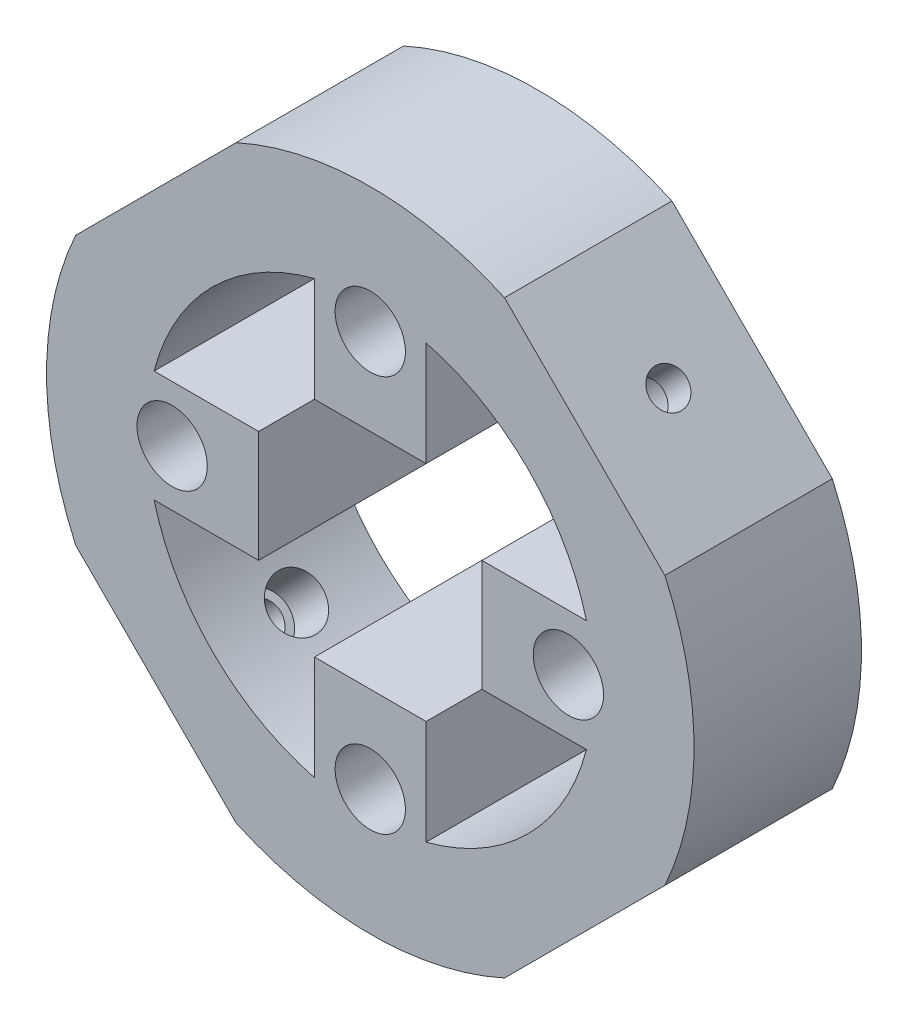
SolidWorks part; units mm, degrees
ref_plane "Front Plane" through (0, 0, 0) normal (0, 0, 1) x (1, 0, 0)
ref_plane "Top Plane" through (0, 0, 0) normal (0, 1, 0) x (1, 0, 0)
ref_plane "Right Plane" through (0, 0, 0) normal (1, 0, 0) x (0, 0, -1)
sketch "Sketch6" plane through (0, 0, 0) normal (0, 0, 1) x (1, 0, 0)
  circle A0 centre (0, 0) radius 20
  circle A1 centre (0, 0) radius 29
  dimension "D1" = 40
  dimension "D2" = 58
extrude "Inner Ring" add sketch "Sketch6" against normal blind 15 separate body
sketch "Sketch7" plane through (0, 0, 0) normal (0, 0, 1) x (1, 0, 0)
  line L2 (-10, 5) -> (-10, -5)
  line L3 (-5, 10) -> (5, 10)
  line L4 (10, 5) -> (10, -5)
  line L5 (-5, -10) -> (5, -10)
  line L14 (-19.3649, 5) -> (-10, 5)
  line L15 (-19.3649, -5) -> (-10, -5)
  line L16 (-5, 19.3649) -> (-5, 10)
  line L17 (5, 19.3649) -> (5, 10)
  line L18 (19.3649, 5) -> (10, 5)
  line L19 (19.3649, -5) -> (10, -5)
  line L20 (5, -19.3649) -> (5, -10)
  line L21 (-5, -19.3649) -> (-5, -10)
  circle A1 centre (0, 0) radius 20
  circle M19 centre (0, 0) radius 20
  dimension "D1" = 20
  dimension "D2" = 20
  dimension "D3" = 10
  dimension "D5" = 10
  dimension "D7" = 10
  dimension "D8" = 10
extrude "Motor Connector Cut" add sketch "Sketch7" against normal blind 15 contours L19 L18 L4 M19 | L17 L16 L3 M19 | L15 L2 L14 M19 | L21 L20 L5 M19
sketch "Sketch9" plane through (0, 0, -15) normal (0, 0, -1) x (-1, 0, 0)
  line L0 (-5, 19.3649) -> (-19.3649, 5)
  line L7 (-5, -19.3649) -> (-19.3649, -5)
  line L8 (5, 19.3649) -> (19.3649, 5)
  line L9 (5, -19.3649) -> (19.3649, -5)
  line L10 (19.3649, -5) -> (26.3895, -12.0246)
  line L11 (5, -19.3649) -> (12.0246, -26.3895)
  line L12 (-19.3649, -5) -> (-26.3895, -12.0246)
  line L13 (-5, -19.3649) -> (-12.0246, -26.3895)
  line L14 (-19.3649, 5) -> (-5, 19.3649)
  line L15 (-5, 19.3649) -> (-12.0246, 26.3895)
  line L16 (-19.3649, 5) -> (-26.3895, 12.0246)
  line L17 (-26.3895, 12.0246) -> (-12.0246, 26.3895)
  line L18 (-26.3895, -12.0246) -> (-12.0246, -26.3895)
  line L19 (12.0246, -26.3895) -> (26.3895, -12.0246)
  line L20 (5, 19.3649) -> (12.0246, 26.3895)
  line L21 (19.3649, 5) -> (26.3895, 12.0246)
  line L22 (26.3895, 12.0246) -> (12.0246, 26.3895)
  circle A2 centre (0, 0) radius 29
  circle A3 centre (0, 0) radius 20
  circle M28 centre (0, 0) radius 29
sketch "Sketch10" plane through (0, 0, -15) normal (0, 0, -1) x (-1, 0, 0)
  circle A3 centre (-17.75, 0) radius 3.15
  circle A4 centre (0, 17.75) radius 3.15
  circle A5 centre (17.75, 0) radius 3.15
  circle A6 centre (0, -17.75) radius 3.15
  dimension "D1" = 6.3
  dimension "D2" = 6.3
  dimension "D4" = 6.3
  dimension "D5" = 6.3
extrude "Cut-Extrude2" cut sketch "Sketch10" against normal blind 70 and the other way blind 55
extrude "Cut-Extrude4" cut sketch "Sketch9" against normal blind 22 contours L17 M28 | L22 M28 | L18 M28 | L19 M28 | A2
sketch "Sketch16" plane through (-19.2071, 19.2071, 0) normal (-0.7071, 0.7071, 0) x (0, 0, 1)
  line L0 (-7.5, 10.1575) -> (-7.5, -10.1575)
  line L1 (0, 10.1575) -> (-15, 10.1575) construction
  line L2 (0, -10.1575) -> (-15, -10.1575) construction
  circle A0 centre (-7.5, 0) radius 2.35
  dimension "D1" = 4.7
extrude "Cut-Extrude6" cut sketch "Sketch16" against normal blind 7.9 contours L0 A0 | L0 A0
sketch "Sketch14" plane through (19.2071, 19.2071, 0) normal (0.7071, 0.7071, 0) x (0, 0, -1)
  line L0 (7.5, 10.1575) -> (7.5, -10.1575)
  line L1 (0, 10.1575) -> (15, 10.1575) construction
  line L2 (0, -10.1575) -> (15, -10.1575) construction
  circle A0 centre (7.5, 0) radius 2.35
  dimension "D1" = 4.7
extrude "Cut-Extrude5" cut sketch "Sketch14" against normal blind 22 contours L0 A0 | L0 A0
sketch "Sketch15" plane through (19.2071, 19.2071, 0) normal (0.7071, 0.7071, 0) x (0, 0, -1)
  line L0 (7.5, 10.1575) -> (7.5, -10.1575)
  line L1 (0, 10.1575) -> (15, 10.1575) construction
  line L2 (0, -10.1575) -> (15, -10.1575) construction
  circle A0 centre (7.5, 0) radius 2.35
  circle A1 centre (7.5, 0) radius 1.65
  circle M1 centre (7.5, 0) radius 2.35
  dimension "D1" = 3.3
extrude "Boss-Extrude1" add sketch "Sketch15" against normal blind 2.9 contours A1 L0 M1 | A1 L0 M1
sketch "Sketch17" plane through (-19.2071, 19.2071, 0) normal (-0.7071, 0.7071, 0) x (0, 0, 1)
  line L0 (-7.5, 2.35) -> (-7.5, -2.35)
  circle A1 centre (-7.5, 0) radius 2.35 construction
  circle A2 centre (-7.5, 0) radius 2.35
  circle A3 centre (-7.5, 0) radius 1.65
  circle M1 centre (-7.5, 0) radius 2.35
  dimension "D1" = 3.3
extrude "Boss-Extrude3" add sketch "Sketch17" against normal blind 2.9 contours A3 L0 M1 | A3 L0 M1
sketch "Sketch20" plane through (-19.2071, -19.2071, 0) normal (-0.7071, -0.7071, 0) x (0, 0, 1)
  line L0 (-7.5, 10.1575) -> (-7.5, -10.1575)
  line L1 (0, 10.1575) -> (-15, 10.1575) construction
  line L2 (0, -10.1575) -> (-15, -10.1575) construction
  circle A0 centre (-7.5, 0) radius 2.35
  dimension "D1" = 4.7
extrude "Cut-Extrude8" cut sketch "Sketch20" against normal blind 9.9 contours L0 A0 | L0 A0
sketch "Sketch18" plane through (19.2071, -19.2071, 0) normal (0.7071, -0.7071, 0) x (0, 0, -1)
  line L0 (7.5, 10.1575) -> (7.5, -10.1575)
  line L1 (0, 10.1575) -> (15, 10.1575) construction
  line L2 (0, -10.1575) -> (15, -10.1575) construction
  circle A0 centre (7.5, 0) radius 2.35
  dimension "D1" = 4.7
extrude "Cut-Extrude7" cut sketch "Sketch18" against normal blind 8.9 contours L0 A0 | L0 A0
sketch "Sketch21" plane through (-19.2071, -19.2071, 0) normal (-0.7071, -0.7071, 0) x (0, 0, 1)
  line L0 (-7.5, 2.35) -> (-7.5, -2.35)
  circle A2 centre (-7.5, 0) radius 2.35 construction
  circle A3 centre (-7.5, 0) radius 2.35 construction
  circle A4 centre (-7.5, 0) radius 2.35
  circle A5 centre (-7.5, 0) radius 1.65
  circle M1 centre (-7.5, 0) radius 2.35
  dimension "D1" = 3.3
extrude "Boss-Extrude5" add sketch "Sketch21" against normal blind 2.9 contours A5 L0 M1 | A5 L0 M1
sketch "Sketch19" plane through (19.2071, -19.2071, 0) normal (0.7071, -0.7071, 0) x (0, 0, -1)
  line L0 (7.5, 2.35) -> (7.5, -2.35)
  circle A0 centre (7.5, 0) radius 2.35 construction
  circle A1 centre (7.5, 0) radius 2.35 construction
  circle A2 centre (7.5, 0) radius 2.35
  circle A3 centre (7.5, 0) radius 1.65
  circle M1 centre (7.5, 0) radius 2.35
  dimension "D1" = 3.3
extrude "Boss-Extrude4" add sketch "Sketch19" against normal blind 2.9 contours A3 L0 M1 | A3 L0 M1
